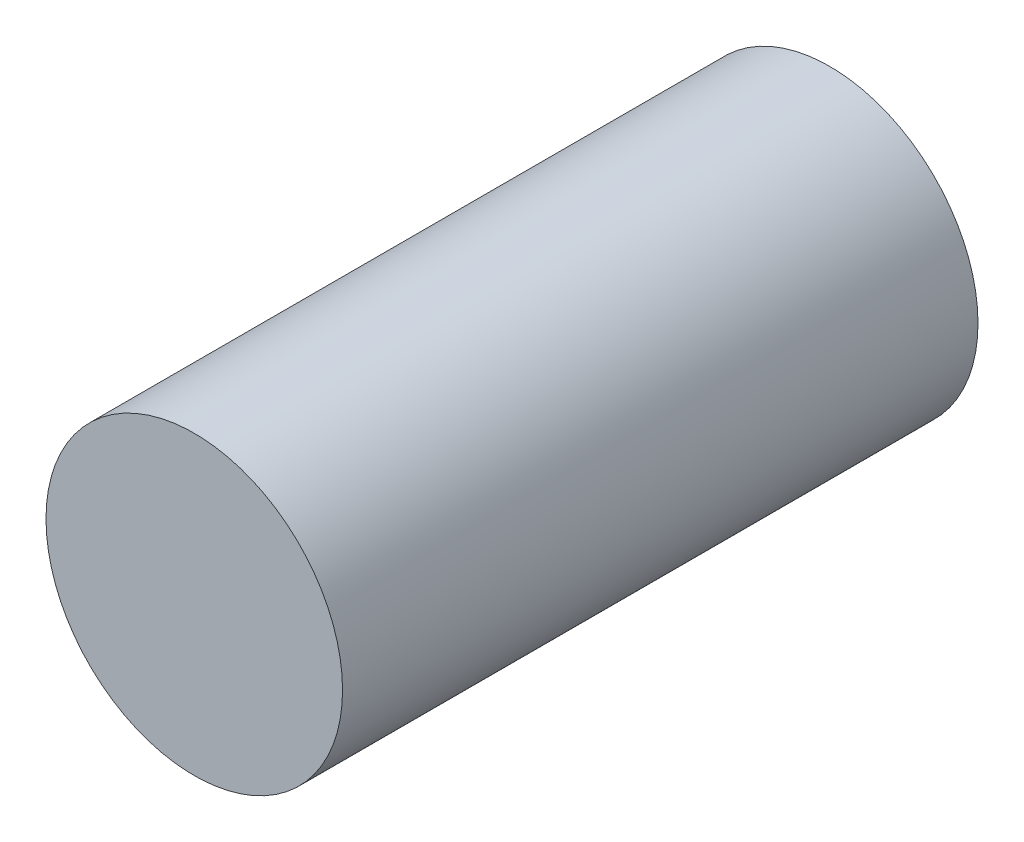
SolidWorks part; units mm, degrees
ref_plane "前视基准面" through (0, 0, 0) normal (0, 0, 1) x (1, 0, 0)
ref_plane "上视基准面" through (0, 0, 0) normal (0, 1, 0) x (1, 0, 0)
ref_plane "右视基准面" through (0, 0, 0) normal (1, 0, 0) x (0, 0, -1)
sketch "草图1" plane through (0, 0, 0) normal (0, 0, 1) x (1, 0, 0)
  circle A0 centre (-11.5854, 17.5649) radius 7
  dimension "D1" = 14
extrude "凸台-拉伸1" add sketch "草图1" along normal blind 30
